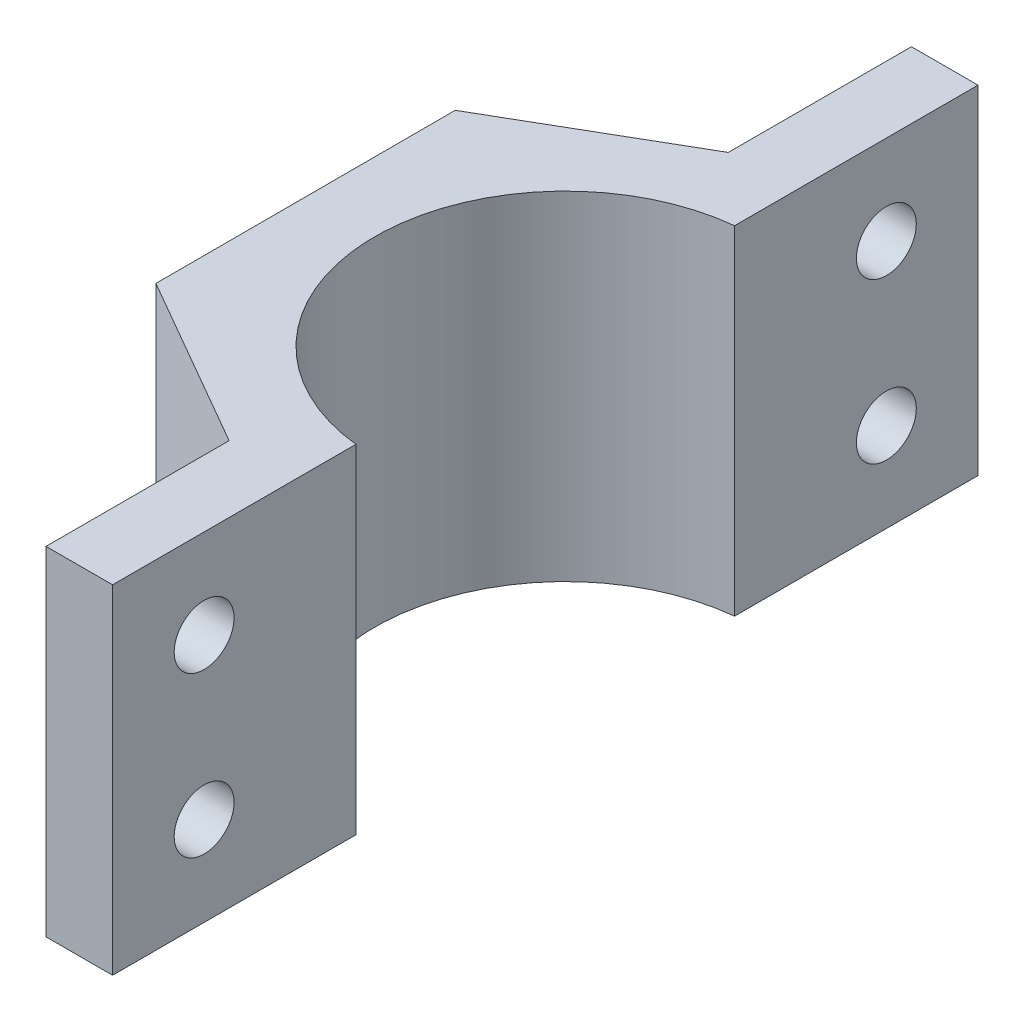
SolidWorks part; units mm, degrees
ref_plane "Front Plane" through (0, 0, 0) normal (0, 0, 1) x (1, 0, 0)
ref_plane "Top Plane" through (0, 0, 0) normal (0, 1, 0) x (1, 0, 0)
ref_plane "Right Plane" through (0, 0, 0) normal (1, 0, 0) x (0, 0, -1)
sketch "Sketch1" plane through (0, 0, 0) normal (0, 1, 0) x (1, 0, 0)
  line L0 (0, -14.3) -> (0, 14.3)
  line L1 (-1.5, 14.2211) -> (-1.5, 21.6429)
  line L2 (-0.0183, 22.5) -> (-19.4947, 11.2342)
  line L3 (-19.4947, 11.2342) -> (-19.4764, -11.2658)
  line L4 (-19.4764, -11.2658) -> (0.0183, -22.5)
  line L5 (0.0183, -22.5) -> (19.4947, -11.2342)
  line L6 (19.4947, -11.2342) -> (19.4764, 11.2658)
  line L7 (19.4764, 11.2658) -> (-0.0183, 22.5)
  line L8 (-1.5, -14.2211) -> (-1.5, -21.6251)
  line L9 (-1.5, 21.6429) -> (-1.5, 32.5035)
  line L10 (-1.5, 32.5035) -> (-6.5, 32.5035)
  line L11 (-6.5, 32.5035) -> (-6.5, 18.7507)
  line L12 (-1.5, -21.6251) -> (-1.5, -32.4965)
  line L13 (-1.5, -32.4965) -> (-6.5, -32.4965)
  line L14 (-6.5, -32.4965) -> (-6.5, -18.7437)
  circle A0 centre (0, 0) radius 14.3
  circle A2 centre (0, 0) radius 19.4856 construction
  point P6 (0, 0)
  dimension "D1" = 28.6
  dimension "D2" = 45
  dimension "D3" = 1.5
  dimension "D4" = 5
  dimension "D5" = 65
extrude "Boss-Extrude1" add sketch "Sketch1" along normal blind 25.4 contours L10 L11 L2 L9 | A0 L1 L2 L3 L4 L8 | L14 L13 L12 L4
sketch "Sketch2" plane through (-6.5, 0, 0) normal (-1, 0, 0) x (0, 0, 1)
  line L0 (25.6201, 25.4) -> (25.6201, 18.7) construction
  line L3 (32.4965, 25.4) -> (18.7437, 25.4) construction
  line L4 (25.6201, 18.7) -> (25.6201, 6.7) construction
  line L5 (25.6201, 6.7) -> (25.6201, 0) construction
  line L6 (32.4965, 0) -> (18.7437, 0) construction
  circle A0 centre (25.6201, 18.7) radius 2.25
  circle A1 centre (25.6201, 6.7) radius 2.25
  dimension "D1" = 4.5
  dimension "D2" = 12
extrude "Cut-Extrude1" cut sketch "Sketch2" against normal through all
mirror "Mirror1" about plane through (0, 0, 0) normal (0, 0, 1) of "Cut-Extrude1"
equation "\"forkdia\"=28.6"
equation "\"D1@Sketch1\"=\"forkdia\""
